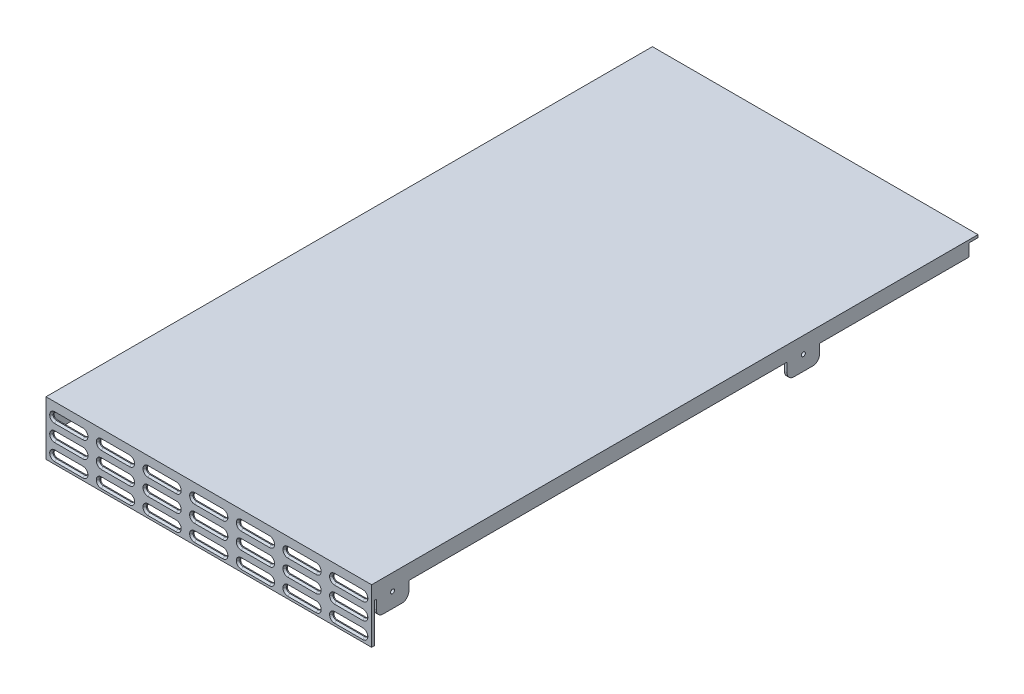
SolidWorks part; units mm, degrees
ref_plane "Front Plane" through (0, 0, 0) normal (0, 0, 1) x (1, 0, 0)
ref_plane "Top Plane" through (0, 0, 0) normal (0, 1, 0) x (1, 0, 0)
ref_plane "Right Plane" through (0, 0, 0) normal (1, 0, 0) x (0, 0, -1)
sketch "Sketch1" plane through (0, 0, 0) normal (1, 0, 0) x (0, 0, -1)
  line L0 (0, 0) -> (0, 19.9898)
  line L1 (0, 19.9898) -> (223.52, 19.9898)
  line L2 (0.9906, 0) -> (0.9906, 18.9992)
  line L3 (0.9906, 18.9992) -> (223.52, 18.9992)
  line L4 (0, 0) -> (0.9906, 0)
  line L5 (223.52, 19.9898) -> (223.52, 18.9992)
  dimension "D1" = 19.9898
  dimension "D2" = 223.52
  dimension "D3" = 0.9906
extrude "Boss-Extrude1" add sketch "Sketch1" along normal blind 120.015
sketch "Sketch2" plane through (0, 18.9992, 0) normal (0, -1, 0) x (1, 0, 0)
  line L0 (0, -0.9906) -> (0, -223.52) construction
  line L1 (0, -0.9906) -> (0.9906, -0.9906)
  line L2 (0, -0.9906) -> (0, -220.2434)
  line L3 (0, -220.2434) -> (0.9906, -220.2434)
  line L4 (0.9906, -0.9906) -> (0.9906, -220.2434)
  line L5 (120.015, -223.52) -> (0, -223.52) construction
  line L6 (120.015, -0.9906) -> (0, -0.9906) construction
  dimension "D1" = 3.2766
  dimension "D2" = 0
  dimension "D3" = 0.9906
extrude "Boss-Extrude2" add sketch "Sketch2" along normal blind 10.4902
ref_plane "Plane1" through (60.0075, 0, 0) normal (-1, 0, 0) x (0, 0, 1)
mirror "Mirror1" about plane through (60.0075, 0, 0) normal (-1, 0, 0) of "Boss-Extrude2"
sketch "Sketch3" plane through (120.015, 0, 0) normal (1, 0, 0) x (0, 0, -1)
  line L1 (220.2434, 14.478) -> (165.1254, 14.478)
  line L2 (220.2434, 14.478) -> (220.2434, 8.509)
  line L3 (220.2434, 8.509) -> (165.1254, 8.509)
  line L4 (165.1254, 14.478) -> (165.1254, 8.509)
  line L5 (0.9906, 8.509) -> (220.2434, 8.509) construction
  line L8 (223.52, 19.9898) -> (0, 19.9898) construction
  dimension "D1" = 55.118
  dimension "D2" = 5.5118
extrude "Cut-Extrude1" cut sketch "Sketch3" against normal up to surface (120.015 mm away) up to face at (0, 11.8745, -111.1885)
sketch "Sketch4" plane through (120.015, 0, 0) normal (1, 0, 0) x (0, 0, -1)
  line L0 (0.9906, 8.509) -> (165.1254, 8.509) construction
  line L1 (1.7272, 8.509) -> (0.9906, 8.509)
  line L2 (1.7272, 8.509) -> (1.7272, 14.478)
  line L3 (1.7272, 14.478) -> (0.9906, 14.478)
  line L4 (0.9906, 8.509) -> (0.9906, 14.478)
  line L5 (0, 19.9898) -> (0, 0) construction
  line L7 (220.2434, 14.478) -> (165.1254, 14.478) construction
  line L8 (0.9906, 0) -> (0.9906, 8.509) construction
  dimension "D1" = 1.7272
  dimension "D2" = 0
  dimension "D3" = 0
extrude "Cut-Extrude2" cut sketch "Sketch4" against normal up to surface (120.015 mm away) up to face at (0, 12.3952, -121.9759)
sketch "Sketch5" plane through (120.015, 0, 0) normal (1, 0, 0) x (0, 0, -1)
  line L0 (1.7272, 8.509) -> (165.1254, 8.509) construction
  line L1 (13.716, 8.509) -> (153.1366, 8.509)
  line L2 (13.716, 8.509) -> (13.716, 14.478)
  line L3 (13.716, 14.478) -> (153.1366, 14.478)
  line L4 (153.1366, 8.509) -> (153.1366, 14.478)
  line L5 (1.7272, 8.509) -> (1.7272, 14.478) construction
  line L6 (1.7272, 14.478) -> (0.9906, 14.478) construction
  line L7 (165.1254, 14.478) -> (165.1254, 8.509) construction
  dimension "D1" = 11.9888
  dimension "D2" = 0
  dimension "D3" = 11.9888
extrude "Cut-Extrude3" cut sketch "Sketch5" against normal up to surface (120.015 mm away) up to face at (0, 12.7423, -101.9344)
hole_wizard "E (0.25) Diameter Hole1" positions "Sketch7" profile "Sketch6" hole size "E" standard "ANSI Inch"
sketch "Sketch7" plane through (120.015, 0, 0) normal (1, 0, 0) x (0, 0, -1)
  line L0 (223.52, 19.9898) -> (0, 19.9898) construction
  line L1 (165.1254, 14.478) -> (165.1254, 8.509) construction
  line L2 (13.716, 14.478) -> (13.716, 8.509) construction
  point P0 (7.7216, 13.9954)
  point P2 (159.131, 13.9954)
  dimension "D1" = 5.9944
  dimension "D2" = 5.9944
  dimension "D3" = 5.9944
  dimension "D4" = 5.9944
sketch "Sketch6" plane through (120.015, 13.9954, -7.7216) normal (0, 1, 0) x (0, 0, -1)
  line L0 (0, 0) -> (0, 2.2282)
  line L1 (0, 2.2282) -> (0.7493, 1.778)
  line L2 (0.7493, 1.778) -> (0.7493, 0)
  line L5 (0.7493, 0) -> (0, 0)
  line L10 (0, 2.2282) -> (-0.7493, 1.778) construction
  line L11 (0, -6.35) -> (0, 107.95) construction
  dimension "Hole Dia." = 1.4986
  dimension "Hole Depth" = 1.778
  dimension "Drill Angle" = 118
mirror "Mirror2" about plane through (60.0075, 0, 0) normal (-1, 0, 0) of "E (0.25) Diameter Hole1"
fillet "Fillet1" radius 2.54 2 edges at (0.4953, 8.509, -153.1366) (0.4953, 8.509, -165.1254)
fillet "Fillet2" radius 2.54 2 edges at (0.4953, 8.509, -13.716) (0.4953, 8.509, -1.7272)
fillet "Fillet3" radius 2.54 2 edges at (119.5197, 8.509, -165.1254) (119.5197, 8.509, -153.1366)
fillet "Fillet4" radius 2.54 2 edges at (119.5197, 8.509, -1.7272) (119.5197, 8.509, -13.716)
sketch "Sketch8" plane through (0, 0, 0) normal (0, 0, 1) x (1, 0, 0)
  line L0 (120.015, 19.9898) -> (0, 19.9898) construction
  line L1 (3.2004, 16.1798) -> (13.6144, 16.1798)
  line L2 (2.0066, 14.986) -> (2.0066, 14.8844)
  line L3 (3.2004, 13.6906) -> (13.6144, 13.6906)
  line L4 (14.8082, 14.986) -> (14.8082, 14.8844)
  line L5 (0, 19.9898) -> (0, 0) construction
  arc A0 (2.0066, 14.986) -> (3.2004, 16.1798) centre (3.2004, 14.986) cw
  arc A1 (3.2004, 13.6906) -> (2.0066, 14.8844) centre (3.2004, 14.8844) cw
  arc A2 (14.8082, 14.8844) -> (13.6144, 13.6906) centre (13.6144, 14.8844) cw
  arc A3 (13.6144, 16.1798) -> (14.8082, 14.986) centre (13.6144, 14.986) cw
  point P10 (2.0066, 16.1798)
  point P17 (14.8082, 16.1798)
  dimension "D5" = 1.1938
  dimension "D6" = 1.1938
  dimension "D7" = 1.1938
  dimension "D8" = 1.1938
  dimension "D1" = 2.4892
  dimension "D2" = 12.8016
  dimension "D3" = 3.81
  dimension "D4" = 2.0066
extrude "Cut-Extrude4" cut sketch "Sketch8" against normal blind 0.9906
chamfer "Chamfer1" distance 0.635 angle 45 8 edges at (14.4585, 14.0403, 0) (8.4074, 13.6906, 0) (2.3563, 14.0403, 0) (14.8082, 14.9352, 0) (2.0066, 14.9352, 0) (14.4585, 15.8301, 0) (2.3563, 15.8301, 0) (8.4074, 16.1798, 0)
pattern_linear "LPattern1" count 7 spacing 17.1958 along (1, 0, 0) count 3 spacing 6.096 along (0, -1, 0) of "Cut-Extrude4", "Chamfer1"
